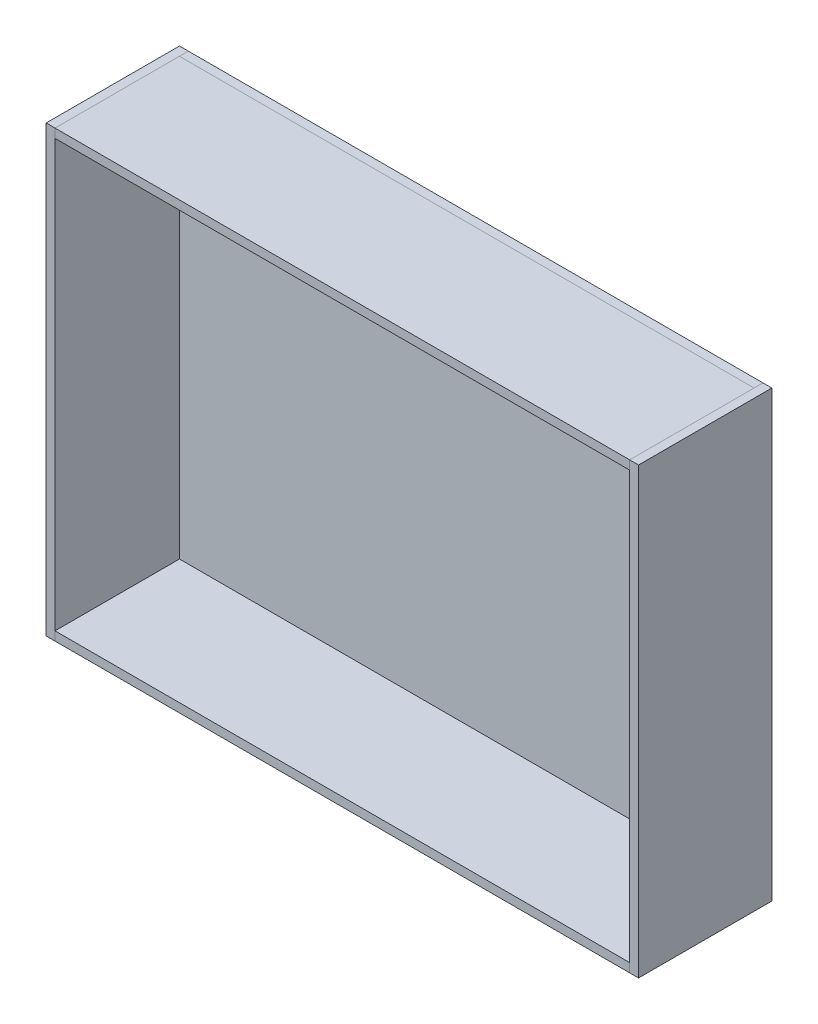
SolidWorks part; units mm, degrees
ref_plane "Plan de face" through (0, 0, 0) normal (0, 0, 1) x (1, 0, 0)
ref_plane "Plan de dessus" through (0, 0, 0) normal (0, 1, 0) x (1, 0, 0)
ref_plane "Plan de droite" through (0, 0, 0) normal (1, 0, 0) x (0, 0, -1)
sketch "Esquisse1" plane through (0, 0, 0) normal (0, 0, 1) x (1, 0, 0)
  line L1 (97, -75) -> (-97, -75)
  line L2 (97, -75) -> (97, 75)
  line L3 (97, 75) -> (-97, 75)
  line L4 (-97, -75) -> (-97, 75)
  line L5 (97, -75) -> (-97, 75) construction
  line L6 (97, 75) -> (-97, -75) construction
  point P0 (0, 0)
  dimension "D1" = 194
  dimension "D2" = 150
extrude "Boss.-Extru.1" add sketch "Esquisse1" along normal blind 3
sketch "Esquisse3" plane through (0, 75, 0) normal (0, 1, 0) x (1, 0, 0)
  line L1 (-97, 0) -> (-100, 0)
  line L2 (-97, 0) -> (-97, -45)
  line L3 (-97, -45) -> (-100, -45)
  line L4 (-100, 0) -> (-100, -45)
  line L5 (97, 0) -> (100, 0)
  line L6 (97, 0) -> (97, -45)
  line L7 (97, -45) -> (100, -45)
  line L8 (100, 0) -> (100, -45)
  dimension "D1" = 3
  dimension "D2" = 3
  dimension "D3" = 45
  dimension "D4" = 45
extrude "Boss.-Extru.3" add sketch "Esquisse3" against normal up to surface (150 mm away) separate body up to face at (0, -75, 1.5)
sketch "Esquisse4" plane through (0, 0, 3) normal (0, 0, 1) x (1, 0, 0)
  line L0 (97, -75) -> (97, 75) construction
  line L1 (-97, 75) -> (97, 75)
  line L2 (-97, 75) -> (-97, 72)
  line L3 (-97, 72) -> (97, 72)
  line L4 (97, 75) -> (97, 72)
  line L5 (-97, 75) -> (-97, -75) construction
  line L6 (97, -75) -> (-97, -75)
  line L7 (97, -75) -> (97, -72)
  line L8 (97, -72) -> (-97, -72)
  line L9 (-97, -75) -> (-97, -72)
  dimension "D1" = 3
  dimension "D2" = 3
extrude "Boss.-Extru.4" add sketch "Esquisse4" along normal up to surface (42 mm away) separate body up to face at (98.5, 0, 45)
